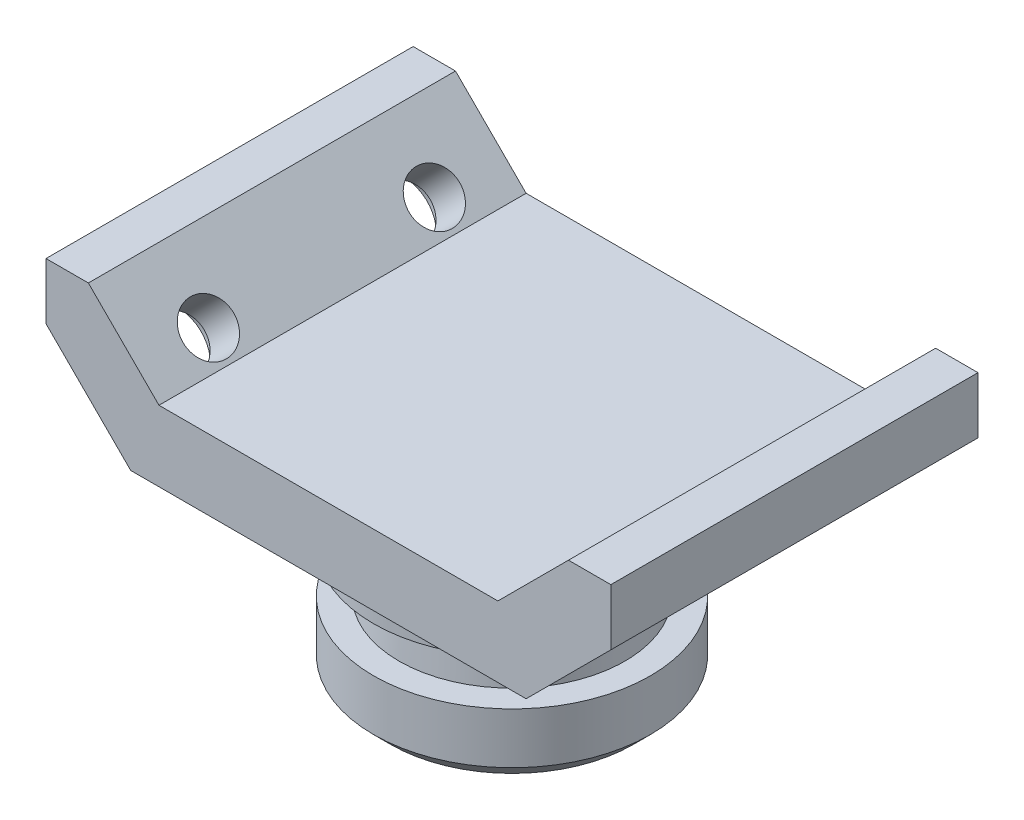
SolidWorks part; units mm, degrees
ref_plane "Alzado" through (0, 0, 0) normal (0, 0, 1) x (1, 0, 0)
ref_plane "Planta" through (0, 0, 0) normal (0, 1, 0) x (1, 0, 0)
ref_plane "Vista lateral" through (0, 0, 0) normal (1, 0, 0) x (0, 0, -1)
sketch "Croquis2" plane through (0, 0, 0) normal (0, 0, 1) x (1, 0, 0)
  line L0 (-30, 0) -> (30, 0)
  line L1 (0, 0) -> (0, -12.5) construction
  line L2 (-35, -12.5) -> (35, -12.5)
  line L3 (30, 0) -> (42.5, 12.5)
  line L4 (42.5, 12.5) -> (50, 12.5)
  line L5 (50, 12.5) -> (50, 2.5)
  line L6 (50, 2.5) -> (35, -12.5)
  line L7 (-50, 2.5) -> (-35, -12.5)
  line L8 (-50, 12.5) -> (-50, 2.5)
  line L9 (-42.5, 12.5) -> (-50, 12.5)
  line L10 (-30, 0) -> (-42.5, 12.5)
  dimension "D1" = 25
  dimension "D2" = 12.5
  dimension "D3" = 15
  dimension "D4" = 7.5
  dimension "D5" = 100
  dimension "D6" = 12.5
extrude "Saliente-Extruir1" add sketch "Croquis2" along normal mid plane 65
sketch "Croquis3" plane through (0, 0, 0) normal (0, 0, 1) x (1, 0, 0)
  line L0 (0, -12.5) -> (-24.5, -12.5)
  line L1 (-35, -12.5) -> (35, -12.5) construction
  line L2 (-24.5, -12.5) -> (-24.5, -22.5)
  line L3 (-21.5, -42.5) -> (0, -42.5)
  line L4 (0, -42.5) -> (0, -12.5)
  line L5 (-24.5, -22.5) -> (-19.5, -22.5)
  line L6 (-19.5, -22.5) -> (-20, -30.4844)
  line L7 (-20, -30.4844) -> (-24.5, -30.4844)
  line L8 (-24.5, -30.4844) -> (-24.5, -39.5)
  line L9 (-24.5, -39.5) -> (-21.5, -42.5)
  point P5 (-24.5, -42.5)
  dimension "D1" = 10
  dimension "D2" = 30
  dimension "D3" = 8
  dimension "D4" = 20
  dimension "D5" = 24.5
revolve "Revolución1" add sketch "Croquis3" angle 360 about L4
sketch "Croquis4" plane through (-23.75, -23.75, 0) normal (-0.7071, -0.7071, 0) x (0, 0, 1)
  line L0 (0, 37.1231) -> (0, 15.9099) construction
  line L1 (32.5, 37.1231) -> (-32.5, 37.1231) construction
  line L2 (32.5, 15.9099) -> (-32.5, 15.9099) construction
  line L6 (0, 26.5165) -> (20, 26.5165) construction
  line L7 (0, 26.5165) -> (-20, 26.5165) construction
  dimension "D1" = 40
hole_wizard "Refrentado para tornillo con cabeza plana de M81" positions "Croquis3D1" profile "Croquis5" counterbore size "M8" standard "ISO" end condition through all
sketch3d "Croquis3D1"
  point P0 (-42.5, -5, -20)
  point P3 (-42.5, -5, 20)
sketch "Croquis5" plane through (-42.5, -5, -20) normal (0, 0, 1) x (0.7071, -0.7071, 0)
  line L0 (0, 0) -> (0, 77.7817)
  line L1 (0, 77.7817) -> (4.5, 77.7817)
  line L3 (4.5, 77.7817) -> (4.5, 5)
  line L4 (4.5, 5) -> (7.5, 5)
  line L5 (7.5, 5) -> (7.5, 0)
  line L7 (7.5, 0) -> (0, 0)
  line L11 (0, -6.35) -> (0, 107.95) construction
  dimension "Diámetro de taladro hasta el siguiente" = 9
  dimension "Profundidad de taladro hasta el siguiente" = 77.7817
  dimension "Diámetro de refrentado" = 15
  dimension "Profundidad de refrentado" = 5
sketch "Croquis6" plane through (0, 0, 0) normal (0, 1, 0) x (1, 0, 0)
  line L0 (0, -32.5) -> (0, 32.5) construction
  line L1 (30, -32.5) -> (-30, -32.5) construction
  line L2 (30, 32.5) -> (-30, 32.5) construction
ref_plane "Plano1" through (0, 0, 0) normal (1, 0, 0) x (0, 0, -1)
mirror "Simetría1" about plane through (0, 0, 0) normal (1, 0, 0) of "Refrentado para tornillo con cabeza plana de M81"
